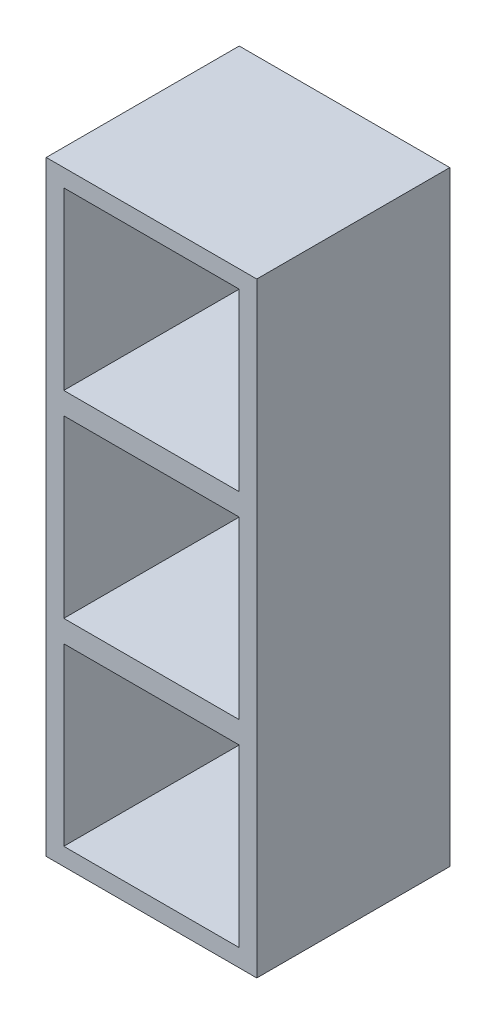
SolidWorks part; units mm, degrees
ref_plane "Alzado" through (0, 0, 0) normal (0, 0, 1) x (1, 0, 0)
ref_plane "Planta" through (0, 0, 0) normal (0, 1, 0) x (1, 0, 0)
ref_plane "Vista lateral" through (0, 0, 0) normal (1, 0, 0) x (0, 0, -1)
sketch "Croquis1" plane through (0, 0, 0) normal (0, 0, 1) x (1, 0, 0)
  line L1 (0, 0) -> (48, 0)
  line L2 (0, 0) -> (0, 138)
  line L3 (0, 138) -> (48, 138)
  line L4 (48, 0) -> (48, 138)
  dimension "D1" = 48
  dimension "D2" = 138
extrude "Saliente-Extruir1" add sketch "Croquis1" along normal blind 44
shell "Vaciado1" thickness 4
sketch "Croquis2" plane through (0, 0, 4) normal (0, 0, 1) x (1, 0, 0)
  line L0 (4, 134) -> (4, 4) construction
  line L1 (4, 49) -> (44, 49)
  line L2 (4, 49) -> (4, 44)
  line L3 (4, 44) -> (44, 44)
  line L4 (44, 49) -> (44, 44)
  line L5 (44, 4) -> (44, 134) construction
  line L6 (4, 4) -> (44, 4) construction
  line L7 (4, 89) -> (44, 89)
  line L8 (4, 94) -> (44, 94)
  line L9 (4, 94) -> (4, 89)
  line L10 (44, 94) -> (44, 89)
  line L11 (4, 44) -> (4, 89) construction
  dimension "D1" = 5
  dimension "D2" = 40
  dimension "D4" = 45
  dimension "D3" = 2
extrude "Saliente-Extruir2" add sketch "Croquis2" along normal through all
